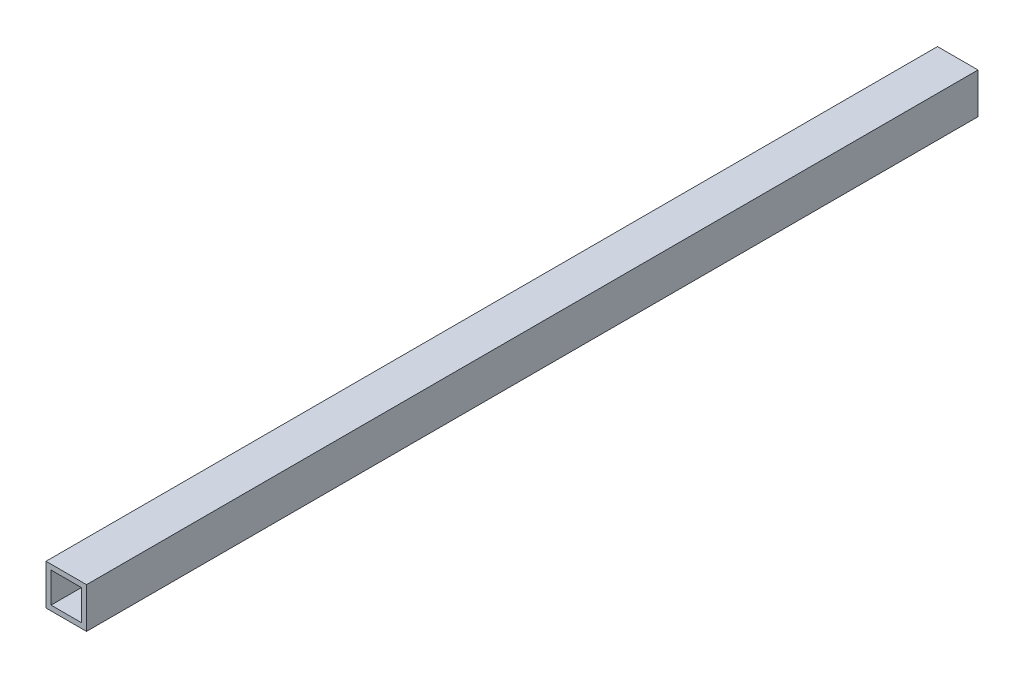
SolidWorks part; units mm, degrees
material "1060 Alloy"
ref_plane "Front Plane" through (0, 0, 0) normal (0, 0, 1) x (1, 0, 0)
ref_plane "Top Plane" through (0, 0, 0) normal (0, 1, 0) x (1, 0, 0)
ref_plane "Right Plane" through (0, 0, 0) normal (1, 0, 0) x (0, 0, -1)
sketch "Sketch1" plane through (0, 0, 0) normal (0, 0, 1) x (1, 0, 0)
  line L0 (3.175, 3.175) -> (3.175, 22.225)
  line L1 (0, 0) -> (25.4, 0)
  line L2 (0, 0) -> (0, 25.4)
  line L3 (0, 25.4) -> (25.4, 25.4)
  line L4 (25.4, 0) -> (25.4, 25.4)
  line L5 (3.175, 22.225) -> (22.225, 22.225)
  line L6 (22.225, 3.175) -> (22.225, 22.225)
  line L7 (3.175, 3.175) -> (22.225, 3.175)
  dimension "D1" = 25.4
  dimension "D2" = 3.175
extrude "Boss-Extrude1" add sketch "Sketch1" along normal blind 558.8
